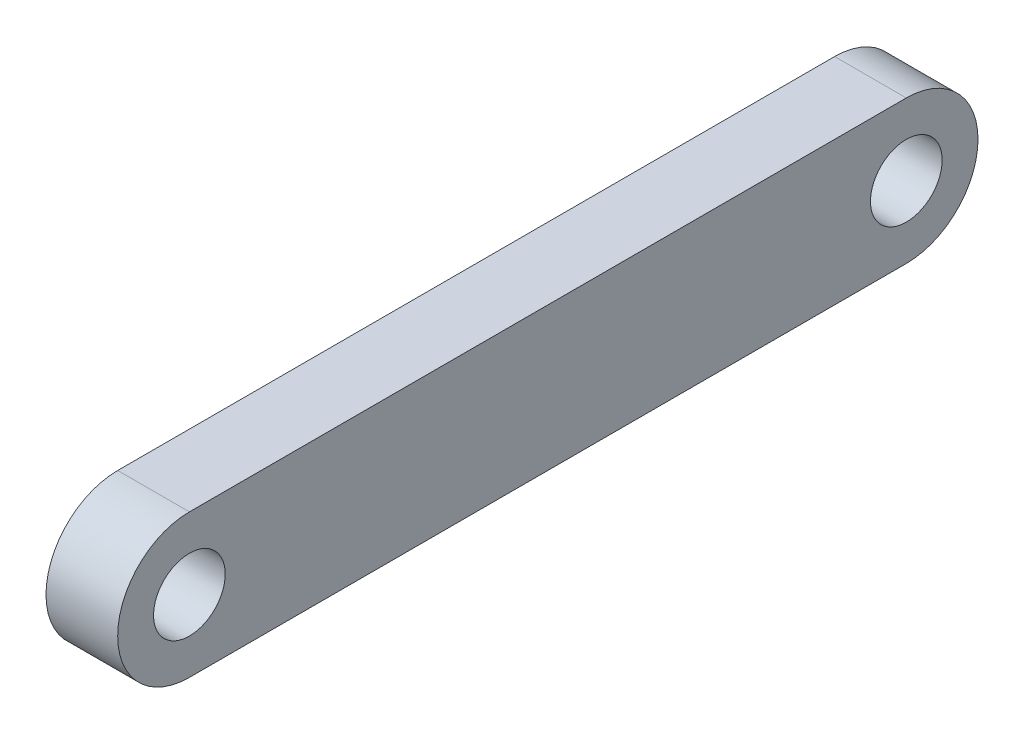
SolidWorks part; units mm, degrees
material "普通碳钢"
ref_plane "前视基准面" through (0, 0, 0) normal (0, 0, 1) x (1, 0, 0)
ref_plane "上视基准面" through (0, 0, 0) normal (0, 1, 0) x (1, 0, 0)
ref_plane "右视基准面" through (0, 0, 0) normal (1, 0, 0) x (0, 0, -1)
sketch "草图1" plane through (0, 0, 0) normal (1, 0, 0) x (0, 0, -1)
  line L0 (-40, 8) -> (40, 8)
  line L1 (-40, -8) -> (40, -8)
  line L2 (0, 0) -> (0, 27.9648) construction
  line L3 (40, 0) -> (0, 0) construction
  line L4 (0, 0) -> (-40, 0) construction
  circle A0 centre (40, 0) radius 4
  arc A1 (-40, -8) -> (-40, 8) centre (-40, 0) cw
  circle A2 centre (-40, 0) radius 4
  arc A3 (40, -8) -> (40, 8) centre (40, 0) ccw
  point P4 (0, 0)
  point P6 (0, -10)
  point P7 (0, 0)
  point P14 (0, 10)
  dimension "D1" = 8
  dimension "D2" = 8
  dimension "D4" = 8
  dimension "D3" = 40
  dimension "D5" = 40
extrude "凸台-拉伸1" add sketch "草图1" along normal blind 8
